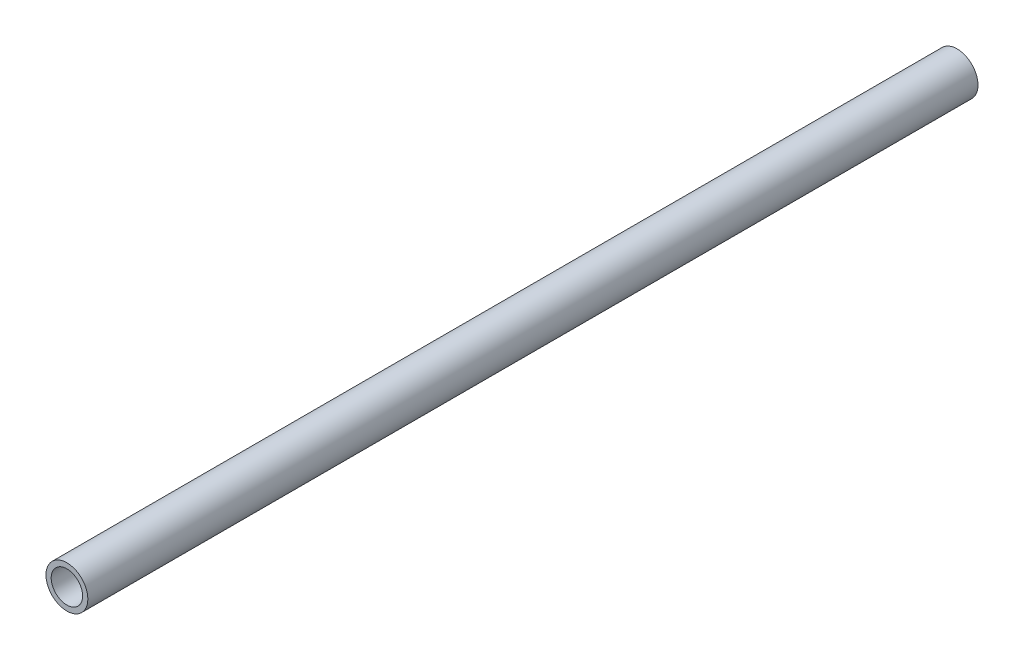
SolidWorks part; units mm, degrees
ref_plane "Front Plane" through (0, 0, 0) normal (0, 0, 1) x (1, 0, 0)
ref_plane "Top Plane" through (0, 0, 0) normal (0, 1, 0) x (1, 0, 0)
ref_plane "Right Plane" through (0, 0, 0) normal (1, 0, 0) x (0, 0, -1)
sketch "Sketch1" plane through (0, 0, 0) normal (0, 0, 1) x (1, 0, 0)
  line L0 (12.7, 0) -> (9.525, 0) construction
  line L1 (-12.7, 0) -> (12.7, 0) construction
  dimension "OD" = 25.4
  dimension "Wall Thickness" = 3.175
sketch "Sketch2" plane through (0, 0, 0) normal (1, 0, 0) x (0, 0, -1)
  line L0 (457.2, 0) -> (-457.2, 0)
  point P4 (0, 0)
  dimension "Length" = 914.4
sketch "Sketch3" plane through (0, 0, 0) normal (0, 0, 1) x (1, 0, 0)
  circle A0 centre (0, 0) radius 12.7
  circle A1 centre (0, 0) radius 9.525
extrude "Boss-Extrude1" add sketch "Sketch3" along normal up to vertex (457.2 mm away) and the other way up to vertex (457.2 mm away) up to point (0, 0, 457.2) other way up to point (0, 0, -457.2)
sketch "Sketch4" plane through (0, 0, 0) normal (1, 0, 0) x (0, 0, -1)
  line L0 (-457.2, 0) -> (-457.2, 12.7) construction
  line L1 (457.2, 0) -> (457.2, 12.7) construction
  line L2 (-457.2, 0) -> (457.2, 0) construction
  line L3 (0, 0) -> (0, 12.7) construction
  line L4 (457.2, 12.7) -> (-457.2, 12.7) construction
  point P8 (-419.1, 0)
  point P9 (419.1, 0)
  dimension "D1" = 914.4
  dimension "D2" = 38.1
sketch "Sketch5" plane through (0, 0, 457.2) normal (0, 0, 1) x (1, 0, 0)
  circle A0 centre (0, 0) radius 12.7
  dimension "D1" = 25.4
extrude "Cut-Extrude1" cut sketch "Sketch5" against normal blind 374.4
equation "\"D1@Cut-Extrude1\"=36in-54cm"
